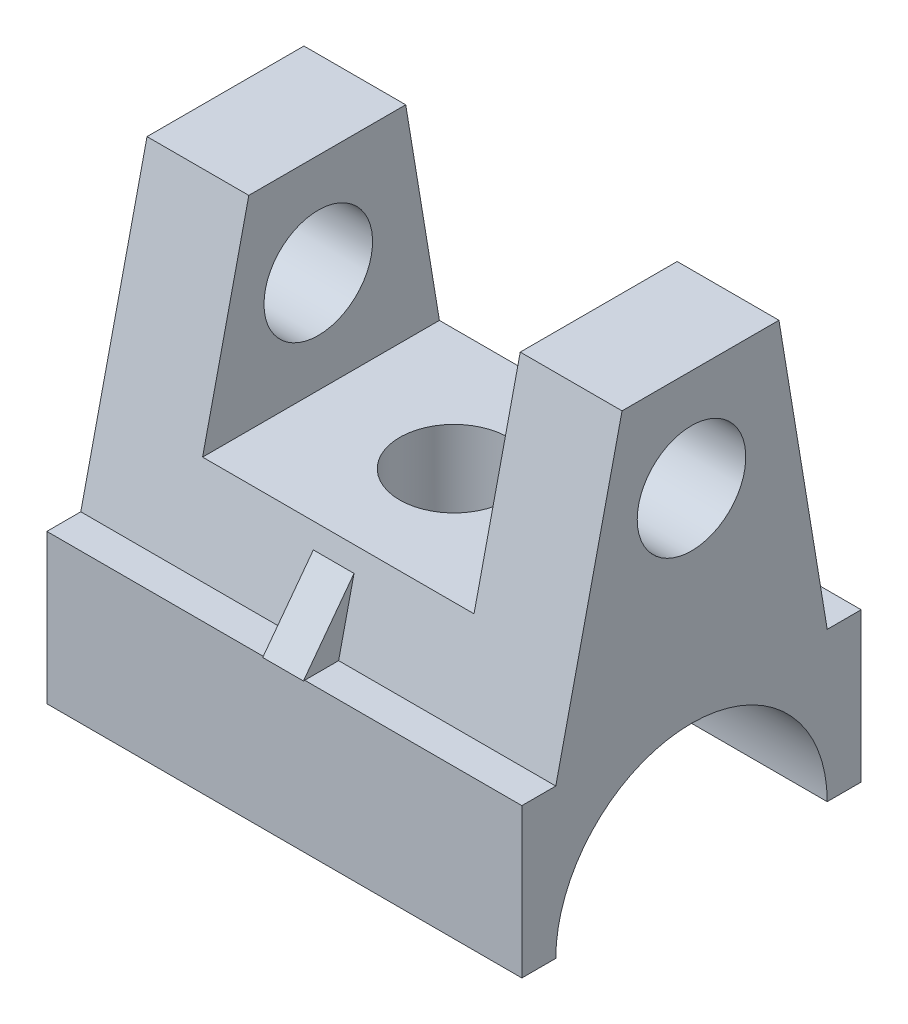
SolidWorks part; units mm, degrees
ref_plane "Front Plane" through (0, 0, 0) normal (0, 0, 1) x (1, 0, 0)
ref_plane "Top Plane" through (0, 0, 0) normal (0, 1, 0) x (1, 0, 0)
ref_plane "Right Plane" through (0, 0, 0) normal (1, 0, 0) x (0, 0, -1)
sketch "Sketch1" plane through (0, 0, 0) normal (0, 1, 0) x (1, 0, 0)
  line L1 (0, 100) -> (140, 100)
  line L2 (0, 100) -> (0, 0)
  line L3 (0, 0) -> (140, 0)
  line L4 (140, 100) -> (140, 0)
  dimension "D1" = 140
  dimension "D2" = 100
extrude "Boss-Extrude1" add sketch "Sketch1" along normal blind 44 contours L2 L1 L4 L3
sketch "Sketch2" plane through (0, 0, 0) normal (-1, 0, 0) x (0, 0, 1)
  line L0 (-100, 0) -> (0, 0) construction
  arc A0 (-90, 0) -> (-10, 0) centre (-50, 0) cw
  dimension "D1" = 40
extrude "Cut-Extrude2" cut sketch "Sketch2" against normal through all and the other way through all flip side to cut
sketch "Sketch3" plane through (0, 0, 0) normal (-1, 0, 0) x (0, 0, 1)
  line L0 (-50, 44) -> (-50, 0) construction
  line L1 (-100, 44) -> (0, 44) construction
  line L2 (-90, 44) -> (-75.7754, 130)
  line L3 (-75.7754, 130) -> (-29.5245, 130)
  line L4 (-29.5245, 130) -> (-10, 44)
  line L5 (-90, 44) -> (-10, 44)
  line L6 (-100, 0) -> (-90, 0) construction
  dimension "D1" = 10
  dimension "D2" = 29.5245
  dimension "D3" = 75.7754
  dimension "D4" = 90
  dimension "D5" = 130
extrude "Boss-Extrude2" add sketch "Sketch3" against normal blind 140
sketch "Sketch5" plane through (0, 0, 0) normal (0, 0, 1) x (1, 0, 0)
  line L0 (140, 130) -> (0, 130) construction
  line L1 (30, 130) -> (110, 130)
  line L2 (30, 130) -> (30, 70)
  line L3 (30, 70) -> (110, 70)
  line L4 (110, 130) -> (110, 70)
  line L5 (140, 44) -> (140, 0) construction
  dimension "D1" = 80
  dimension "D2" = 60
  dimension "D3" = 30
extrude "Cut-Extrude3" cut sketch "Sketch5" against normal through all both and the other way through all
sketch "Sketch6" plane through (0, 70, 0) normal (0, 1, 0) x (1, 0, 0)
  line L0 (30, 85.6995) -> (30, 15.9028) construction
  line L1 (110, 85.6995) -> (30, 85.6995) construction
  circle A0 centre (70, 50) radius 16
  dimension "D1" = 32
  dimension "D2" = 40
  dimension "D3" = 80
  dimension "D4" = 35.6995
extrude "Cut-Extrude4" cut sketch "Sketch6" against normal through all both
sketch "Sketch7" plane through (0, 0, 0) normal (-1, 0, 0) x (0, 0, 1)
  line L0 (0, 44) -> (0, 0) construction
  line L1 (-10, 44) -> (0, 44) construction
  circle A0 centre (-50, 100) radius 16
  dimension "D1" = 32
  dimension "D2" = 50
  dimension "D3" = 56
extrude "Cut-Extrude5" cut sketch "Sketch7" against normal through all both
ref_plane "Plane2" through (70, 0, 0) normal (-1, 0, 0) x (0, 0, 1)
ref_plane "Plane3" through (0, 64, 0) normal (0, 1, 0) x (1, 0, 0)
sketch "Sketch15" plane through (70, 0, 0) normal (-1, 0, 0) x (0, 0, 1)
  line L0 (-14.5406, 64) -> (-10, 44)
  line L3 (-14.5406, 64) -> (0.3803, 44)
  line L4 (0.3803, 44) -> (-10, 44)
  line L5 (55.2196, 64) -> (-55.2196, 64) construction
  line L6 (-10, 44) -> (-29.5245, 130) construction
  dimension "D1" = 0.3803
extrude "Boss-Extrude6" add sketch "Sketch15" along normal mid plane 12 contours L4 L0 L3
sketch "Sketch17" plane through (70, 0, 0) normal (-1, 0, 0) x (0, 0, 1)
  line L0 (-86.6919, 64) -> (-100.019, 44)
  line L1 (55.2196, 64) -> (-55.2196, 64) construction
  line L2 (-85.6995, 70) -> (-75.7754, 130) construction
  line L3 (-86.6919, 64) -> (-90, 44)
  line L4 (-90, 44) -> (-100.019, 44)
  dimension "D1" = 90
  dimension "D2" = 100.019
  dimension "D3" = 44
extrude "Boss-Extrude7" add sketch "Sketch17" along normal mid plane 12 contours L4 L0 L3
